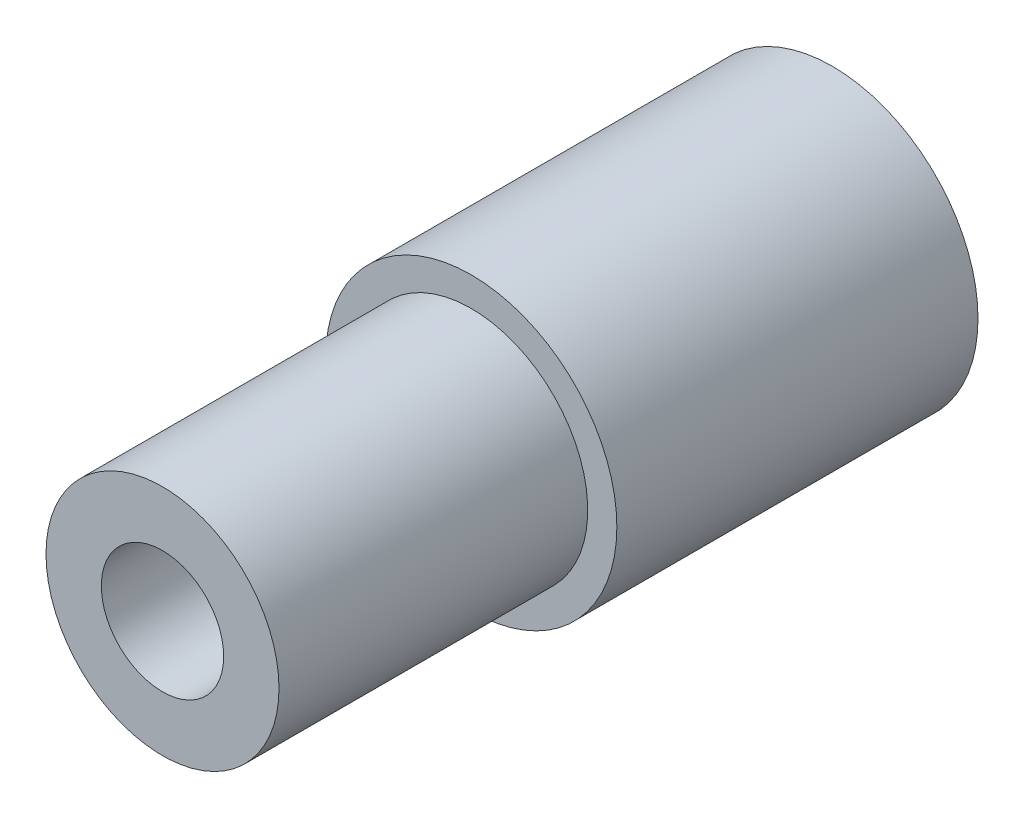
SolidWorks part; units mm, degrees
material "3003 Alloy"
ref_plane "Front Plane" through (0, 0, 0) normal (0, 0, 1) x (1, 0, 0)
ref_plane "Top Plane" through (0, 0, 0) normal (0, 1, 0) x (1, 0, 0)
ref_plane "Right Plane" through (0, 0, 0) normal (1, 0, 0) x (0, 0, -1)
sketch "Sketch2" plane through (0, 0, 0) normal (0, 0, 1) x (1, 0, 0)
  circle A0 centre (0, 0) radius 4
  circle A1 centre (0, 0) radius 2.1
  dimension "D1" = 8
  dimension "D2" = 4.2
extrude "Boss-Extrude1" add sketch "Sketch2" along normal blind 23
sketch "Sketch3" plane through (0, 0, 0) normal (0, 0, -1) x (-1, 0, 0)
  circle A0 centre (0, 0) radius 4 construction
  circle A1 centre (0, 0) radius 4
  circle A2 centre (0, 0) radius 5
  dimension "D1" = 10
extrude "Boss-Extrude2" add sketch "Sketch3" against normal blind 12.4
